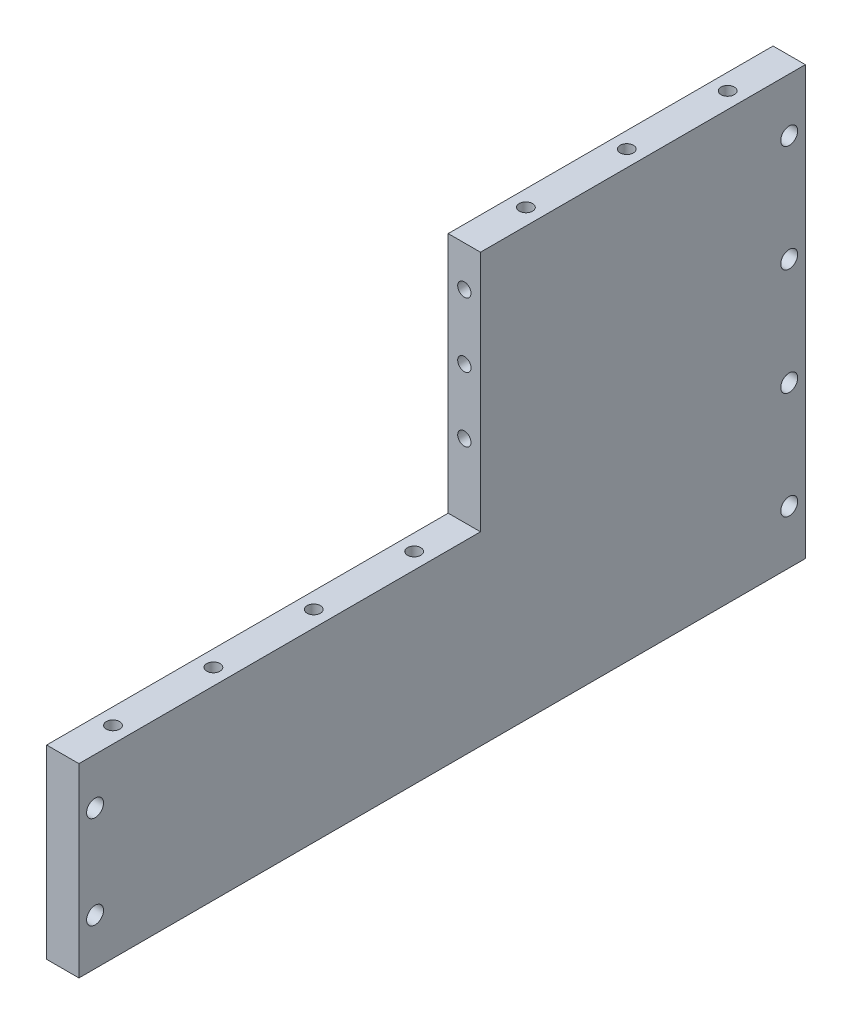
SolidWorks part; units mm, degrees
ref_plane "Front Plane" through (0, 0, 0) normal (0, 0, 1) x (1, 0, 0)
ref_plane "Top Plane" through (0, 0, 0) normal (0, 1, 0) x (1, 0, 0)
ref_plane "Right Plane" through (0, 0, 0) normal (1, 0, 0) x (0, 0, -1)
sketch "Sketch1" plane through (0, 0, 0) normal (1, 0, 0) x (0, 0, -1)
  line L1 (-90, 53) -> (90, 53)
  line L2 (-90, 53) -> (-90, -53)
  line L3 (-90, -53) -> (90, -53)
  line L4 (90, 53) -> (90, -53)
  line L5 (-90, 53) -> (90, -53) construction
  line L6 (-90, -53) -> (90, 53) construction
  line L11 (-90, 53) -> (9.5, 53)
  line L12 (-90, 53) -> (-90, -7)
  line L13 (-90, -7) -> (9.5, -7)
  line L14 (9.5, 53) -> (9.5, -7)
  line L21 (82, 0) -> (90, 0) construction
  line L22 (90, 53) -> (82, 53)
  line L23 (90, 53) -> (90, -53)
  line L24 (90, -53) -> (82, -53)
  line L25 (82, 53) -> (82, -53)
  line L26 (86, 0) -> (86, 53) construction
  line L27 (-82, -30) -> (-90, -30) construction
  line L28 (-90, -7) -> (-82, -7)
  line L29 (-90, -7) -> (-90, -53)
  line L30 (-90, -53) -> (-82, -53)
  line L31 (-82, -7) -> (-82, -53)
  line L32 (-86, -30) -> (-86, -7) construction
  circle A5 centre (86, 39.75) radius 2.1
  circle A6 centre (86, 13.25) radius 2.1
  circle A7 centre (86, -13.25) radius 2.1
  circle A8 centre (86, -39.75) radius 2.1
  circle A9 centre (-86, -18.5) radius 2.1
  circle A10 centre (-86, -41.5) radius 2.1
  point P0 (0, 0)
  point P42 (-82, -30)
  dimension "D10" = 26.5
  dimension "D5" = 4.2
  dimension "D1" = 106
  dimension "D2" = 180
  dimension "D3" = 99.5
  dimension "D4" = 60
  dimension "D9" = 8
  dimension "D11" = 13.25
  dimension "D13" = 8
extrude "Boss-Extrude1" add sketch "Sketch1" against normal blind 8 contours L31 L13 L2 L3 A9 A10 | L13 L31 L3 L25 L1 L14 | L1 L25 L3 L4 A7 A6 A5 A8
sketch "Sketch2" plane through (0, -53, 0) normal (0, -1, 0) x (1, 0, 0)
  line L0 (0, 90) -> (0, -90) construction
  line L2 (-8, -90) -> (0, -90)
  line L8 (-8, -90) -> (-8, -0.5)
  line L9 (-8, -0.5) -> (0, -0.5)
  line L10 (0, -90) -> (0, -0.5)
  line L11 (-4, -0.5) -> (-4, -90) construction
  line L12 (-8, -45.25) -> (0, -45.25) construction
  circle A7 centre (-4, -86) radius 1.65
  circle A8 centre (-4, -4.5) radius 1.65
  circle A9 centre (-4, -45.25) radius 1.65
  dimension "D2" = 3.3
  dimension "D1" = 89.5
  dimension "D3" = 4
extrude "Cut-Extrude1" cut sketch "Sketch2" against normal blind 5
sketch "Sketch3" plane through (0, 53, 0) normal (0, 1, 0) x (1, 0, 0)
  line L0 (-8, 49.75) -> (0, 49.75) construction
  line L1 (-8, 9.5) -> (-8, 90) construction
  line L2 (0, 9.5) -> (0, 90) construction
  circle A0 centre (-4, 49.75) radius 1.65
  circle A1 centre (-4, 74.75) radius 1.65
  circle A2 centre (-4, 24.75) radius 1.65
  dimension "D1" = 3.3
  dimension "D2" = 25
extrude "Cut-Extrude2" cut sketch "Sketch3" against normal blind 10
sketch "Sketch4" plane through (0, -7, 0) normal (0, 1, 0) x (1, 0, 0)
  line L0 (-4, -15.375) -> (-4, 9.5) construction
  line L5 (-8, -40.25) -> (0, -40.25) construction
  line L6 (-8, -90) -> (-8, 9.5) construction
  line L7 (0, -90) -> (0, 9.5) construction
  line L9 (-4, -15.375) -> (-4, -40.25) construction
  line L10 (-8, 9.5) -> (0, 9.5) construction
  circle A1 centre (-4, -2.9375) radius 1.65
  circle A2 centre (-4, -27.8125) radius 1.65
  circle A3 centre (-4, -52.6875) radius 1.65
  circle A4 centre (-4, -77.5625) radius 1.65
  dimension "D1" = 3.3
extrude "Cut-Extrude3" cut sketch "Sketch4" against normal blind 10
sketch "Sketch5" plane through (0, 0, -9.5) normal (0, 0, 1) x (1, 0, 0)
  line L0 (0, 53) -> (0, -7) construction
  line L1 (-8, 53) -> (0, 53)
  line L2 (-8, 53) -> (-8, 1)
  line L3 (-8, 1) -> (0, 1)
  line L4 (0, 53) -> (0, 1)
  line L5 (-8, -7) -> (0, -7) construction
  line L7 (-8, 27) -> (0, 27) construction
  circle A1 centre (-4, 11) radius 1.65
  circle A2 centre (-4, 43) radius 1.65
  circle A3 centre (-4, 27) radius 1.65
  point P7 (-4, 1)
  point P10 (-4, -7)
  dimension "D2" = 3.3
  dimension "D1" = 8
  dimension "D3" = 10
extrude "Cut-Extrude4" cut sketch "Sketch5" against normal blind 10 contours A2 | A3 | A1
